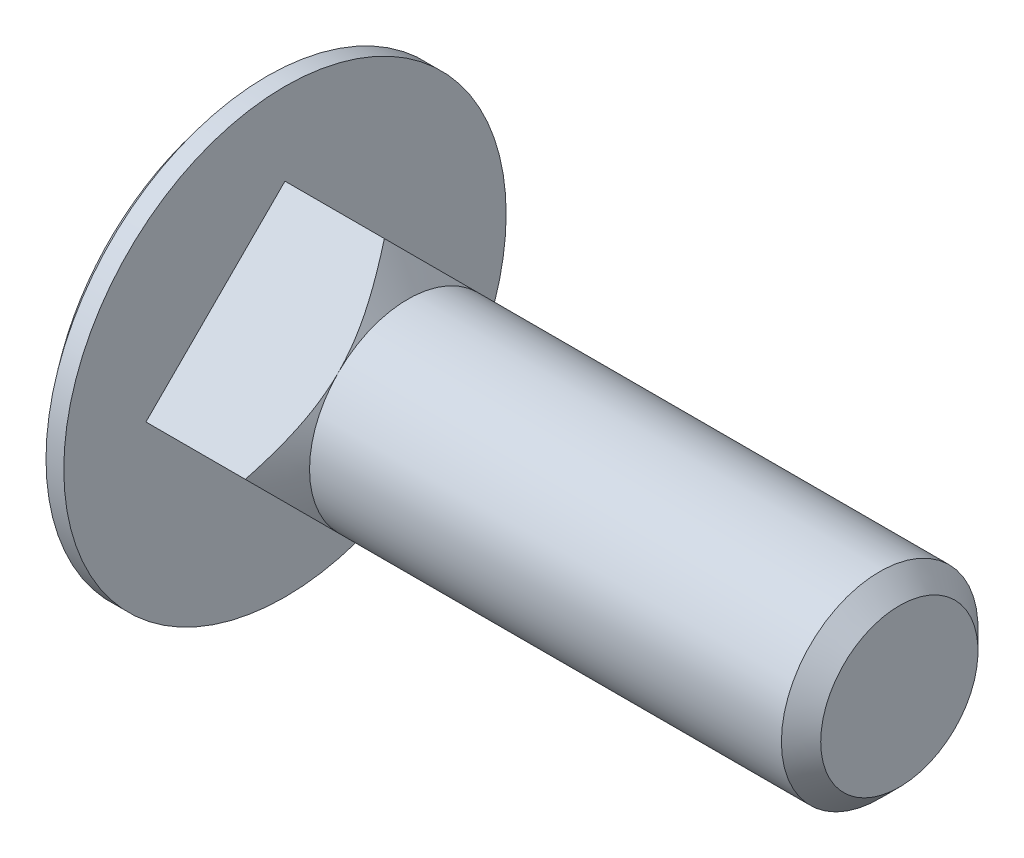
SolidWorks part; units mm, degrees
material "AISI 1020"
ref_plane "Спереди" through (0, 0, 0) normal (0, 0, 1) x (1, 0, 0)
ref_plane "Сверху" through (0, 0, 0) normal (0, 1, 0) x (1, 0, 0)
ref_plane "Справа" through (0, 0, 0) normal (1, 0, 0) x (0, 0, -1)
sketch "Эскиз1" plane through (0, 0, 0) normal (0, 0, 1) x (1, 0, 0)
  line L0 (-168.009, 0) -> (8232.4431, 0) construction
  line L1 (-0.7238, 9) -> (0, 9)
  line L2 (0, 9) -> (0, 4)
  line L3 (0, 4) -> (25, 4)
  line L4 (25, 4) -> (25, 0)
  line L5 (25, 0) -> (-4, 0)
  line L6 (25, 0) -> (25, -20) construction
  line L7 (0, 9) -> (5, 9) construction
  line L8 (5, 9) -> (25, 9) construction
  arc A0 (-4, 0) -> (-0.7238, 9) centre (10, 0) cw
  dimension "_R" = 14
  dimension "_d_" = 8
  dimension "_D" = 18
  dimension "_k" = 4
  dimension "_l" = 25
  dimension "_l_" = 20
  dimension "_f" = 5
  dimension "_b" = 20
revolve "Повернуть1" add sketch "Эскиз1" angle 360 about L0
cosmetic thread "Условное изображение резьбы1" parameters "D1"=20, "D2"=4.11
sketch "Эскиз2" plane through (0, 0, 0) normal (1, 0, 0) x (0, 0, -1)
  line L1 (0, 5.6569) -> (-5.6569, 0)
  line L2 (-5.6569, 0) -> (0, -5.6569)
  line L3 (0, -5.6569) -> (5.6569, 0)
  line L4 (5.6569, 0) -> (0, 5.6569)
  circle A0 centre (0, 0) radius 4 construction
  dimension "_V" = 8
extrude "Бобышка-Вытянуть1" add sketch "Эскиз2" along normal up to vertex (5 mm away) up to point (5, 9, 0)
sketch "Эскиз3" plane through (0, 0, 0) normal (0, 0, 1) x (1, 0, 0)
  line L0 (-1000, 0) -> (49000, 0) construction
  line L1 (5, 4) -> (4.0434, 5.6569)
  line L2 (4.0434, 5.6569) -> (5, 5.6569)
  line L3 (5, 5.6569) -> (5, 4)
  line L4 (5, 5.6569) -> (0, 5.6569) construction
  line L5 (25, 4) -> (5, 4) construction
  line L6 (5, 5.6569) -> (5, 2.8284) construction
  dimension "D1" = 30
revolve "Вырез-Повернуть1" cut sketch "Эскиз3" angle 360 about L0
chamfer "Фаска1" distance 0.8 angle 45 1 edges at (25, 0, 4)
equation "\"_l@Эскиз1\"=\"_f@Эскиз1\"+\"_l_@Эскиз1\""
equation "\"_b\"=7.5"
equation "\"D1@Условное изображение резьбы1\"=\"_b@Эскиз1\""
equation "\"D1@Фаска1\"=\"_d_@Эскиз1\"/10"
